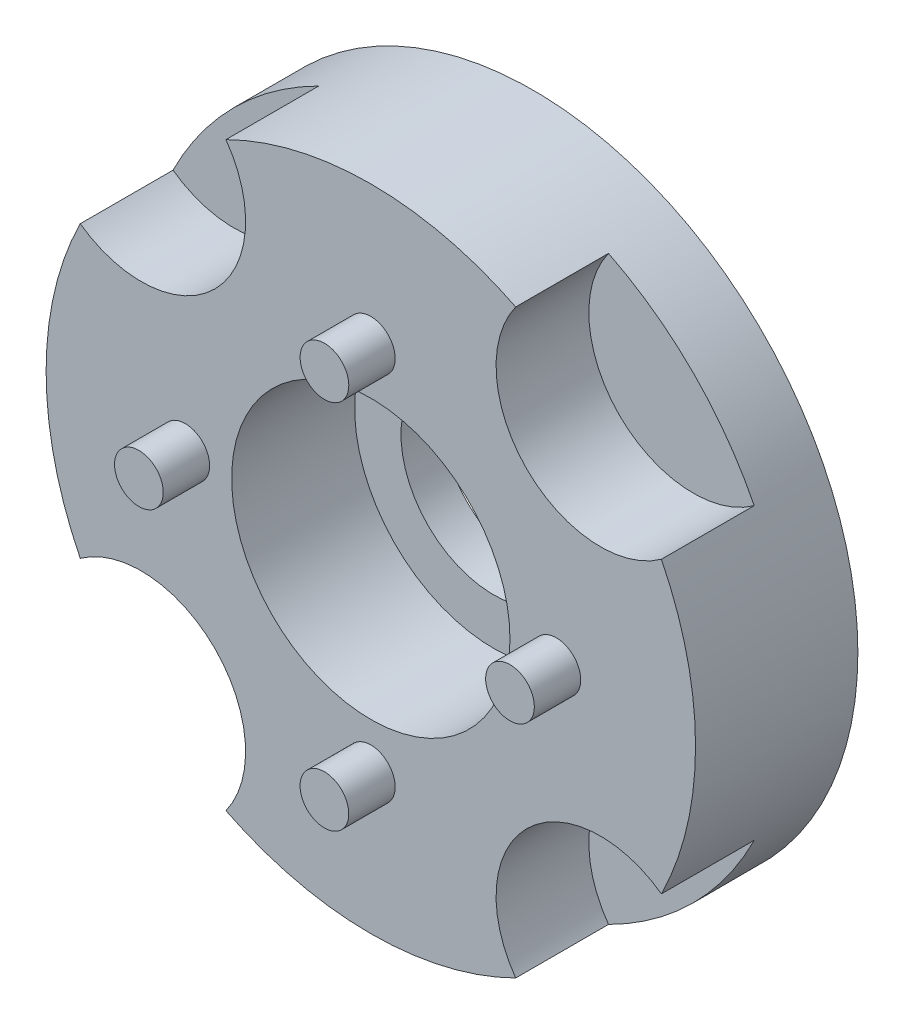
SolidWorks part; units mm, degrees
ref_plane "Ebene vorne" through (0, 0, 0) normal (0, 0, 1) x (1, 0, 0)
ref_plane "Ebene oben" through (0, 0, 0) normal (0, 1, 0) x (1, 0, 0)
ref_plane "Ebene rechts" through (0, 0, 0) normal (1, 0, 0) x (0, 0, -1)
sketch "Skizze1" plane through (0, 0, 0) normal (0, 0, 1) x (1, 0, 0)
  circle A0 centre (0, 0) radius 7
  dimension "D1" = 14
extrude "Aufsatz-Linear austragen1" add sketch "Skizze1" along normal blind 3.5
sketch "Skizze2" plane through (0, 0, 3.5) normal (0, 0, 1) x (1, 0, 0)
  circle A0 centre (0, 4) radius 0.525
  dimension "D1" = 1.05
  dimension "D2" = 4
extrude "Aufsatz-Linear austragen2" add sketch "Skizze2" along normal blind 1
pattern_circular "Kreismuster1" count 4 over 360 about axis through (0, 0, 0) along (0, 0, 1) of "Aufsatz-Linear austragen2"
sketch "Skizze3" plane through (0, 0, 3.5) normal (0, 0, 1) x (1, 0, 0)
  circle A0 centre (0, 0) radius 3
  dimension "D1" = 6
extrude "Schnitt-Linear austragen1" cut sketch "Skizze3" against normal blind 2.65 and the other way through all
sketch "Skizze4" plane through (0, 0, 0.85) normal (0, 0, 1) x (1, 0, 0)
  circle A0 centre (0, 0) radius 2
  dimension "D1" = 4
extrude "Schnitt-Linear austragen2" cut sketch "Skizze4" against normal through all
sketch "Skizze5" plane through (0, 0, 3.5) normal (0, 0, 1) x (1, 0, 0)
  line L0 (0, 0) -> (-4.9497, 4.9497) construction
  line L1 (2.475, 0) -> (-2.475, 0) construction
  circle A0 centre (0, 0) radius 7 construction
  circle A1 centre (-4.9497, 4.9497) radius 2.25
  dimension "D2" = 4.5
  dimension "D1" = 45
extrude "Schnitt-Linear austragen3" cut sketch "Skizze5" against normal blind 2
pattern_circular "Kreismuster2" count 4 over 360 about axis through (0, 0, 0) along (0, 0, 1) of "Schnitt-Linear austragen3"
